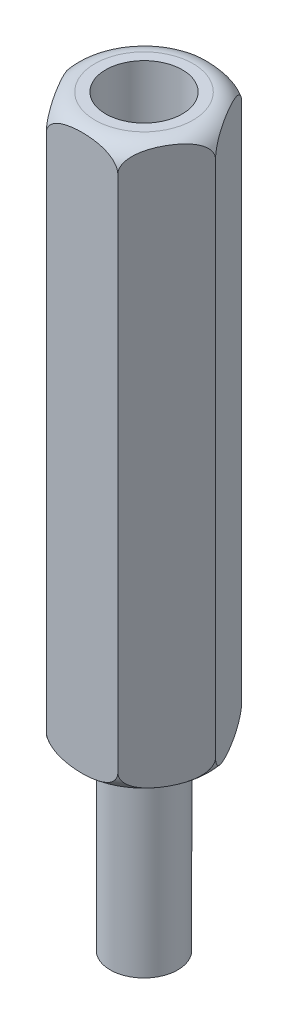
SolidWorks part; units mm, degrees
material "Brass"
ref_plane "Front Plane" through (0, 0, 0) normal (0, 0, 1) x (1, 0, 0)
ref_plane "Top Plane" through (0, 0, 0) normal (0, 1, 0) x (1, 0, 0)
ref_plane "Right Plane" through (0, 0, 0) normal (1, 0, 0) x (0, 0, -1)
sketch "Sketch1" plane through (0, 0, 0) normal (0, 1, 0) x (1, 0, 0)
  line L1 (3.1754, 0) -> (1.5877, 2.75)
  line L2 (1.5877, 2.75) -> (-1.5877, 2.75)
  line L3 (-1.5877, 2.75) -> (-3.1754, 0)
  line L4 (-3.1754, 0) -> (-1.5877, -2.75)
  line L5 (-1.5877, -2.75) -> (1.5877, -2.75)
  line L6 (1.5877, -2.75) -> (3.1754, 0)
  circle A0 centre (0, 0) radius 2.75 construction
  dimension "D1" = 5.5
extrude "Boss-Extrude1" add sketch "Sketch1" along normal blind 25
hole_wizard "M3 Clearance Hole1" positions "Sketch3" profile "Sketch2" hole size "M3" standard "ISO"
sketch "Sketch3" plane through (0, 25, 0) normal (0, 1, 0) x (-1, 0, 0)
  point P0 (0, 0)
sketch "Sketch2" plane through (0, 25, 0) normal (1, 0, 0) x (0, 0, 1)
  line L0 (0, 0) -> (0, 13.0215)
  line L1 (0, 13.0215) -> (1.7, 12)
  line L2 (1.7, 12) -> (1.7, 0)
  line L5 (1.7, 0) -> (0, 0)
  line L10 (0, 13.0215) -> (-1.7, 12) construction
  line L11 (0, -6.35) -> (0, 107.95) construction
  dimension "Hole Dia." = 3.4
  dimension "Hole Depth" = 12
  dimension "Drill Angle" = 118
sketch "Sketch4" plane through (0, 0, 0) normal (0, 0, 1) x (1, 0, 0)
  line L0 (-3.1754, 25) -> (-3.1754, 0) construction
  line L1 (-3.1754, 25) -> (-1.5877, 25) construction
  line L4 (-3.1754, 0) -> (-1.5877, 0) construction
  line L6 (-2.1754, 25) -> (-3.1754, 25)
  line L7 (-3.1754, 25) -> (-3.1754, 24)
  line L8 (-3.1754, 1) -> (-3.1754, 0)
  line L9 (-3.1754, 0) -> (-2.1754, 0)
  line L14 (0, 25) -> (0, 0) construction
  line L15 (-1.5877, 25) -> (1.5877, 25) construction
  arc A0 (-3.1754, 24) -> (-2.1754, 25) centre (-2.1754, 24) cw
  arc A2 (-3.1754, 1) -> (-2.1754, 0) centre (-2.1754, 1) ccw
  dimension "D1" = 1
revolve "Cut-Revolve1" cut sketch "Sketch4" angle 360 about L14
sketch "Sketch5" plane through (0, 0, 0) normal (0, -1, 0) x (1, 0, 0)
  circle A0 centre (0, 0) radius 1.5
  dimension "D1" = 3
extrude "Boss-Extrude2" add sketch "Sketch5" along normal blind 8
